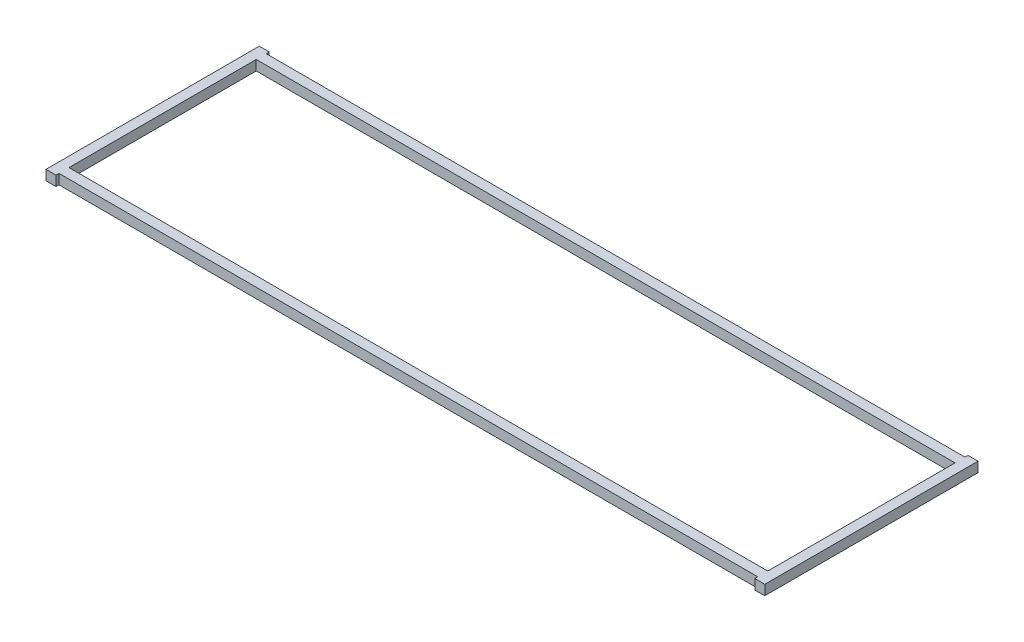
SolidWorks part; units mm, degrees
ref_plane "Front" through (0, 0, 0) normal (0, 0, 1) x (1, 0, 0)
ref_plane "Top" through (0, 0, 0) normal (0, 1, 0) x (1, 0, 0)
ref_plane "Right" through (0, 0, 0) normal (1, 0, 0) x (0, 0, -1)
sketch "Sketch1" plane through (0, 0, 0) normal (0, 1, 0) x (1, 0, 0)
  line L0 (222.25, 67.8212) -> (228.6, 67.8212)
  line L1 (-228.6, 67.8212) -> (-222.25, 67.8212)
  line L2 (-228.6, 67.8212) -> (-228.6, -67.8212)
  line L3 (-228.6, -67.8212) -> (-222.25, -67.8212)
  line L4 (228.6, 67.8212) -> (228.6, -67.8212)
  line L5 (-228.6, 67.8212) -> (228.6, -67.8212) construction
  line L6 (-228.6, -67.8212) -> (228.6, 67.8212) construction
  line L8 (-222.25, 67.8212) -> (-222.25, 65.913)
  line L9 (-222.25, 65.913) -> (222.25, 65.913)
  line L10 (222.25, 67.8212) -> (222.25, 65.913)
  line L12 (-222.25, -67.8212) -> (-222.25, -65.913)
  line L13 (-222.25, -65.913) -> (222.25, -65.913)
  line L14 (222.25, -67.8212) -> (222.25, -65.913)
  line L15 (222.25, -67.8212) -> (228.6, -67.8212)
  line L17 (-222.25, -59.563) -> (222.25, -59.563)
  line L18 (-222.25, -59.563) -> (-222.25, 59.563)
  line L19 (-222.25, 59.563) -> (222.25, 59.563)
  line L20 (222.25, -59.563) -> (222.25, 59.563)
  line L21 (-222.25, -59.563) -> (222.25, 59.563) construction
  line L22 (-222.25, 59.563) -> (222.25, -59.563) construction
  point P0 (0, 0)
  point P14 (0, 0)
  dimension "D1" = 457.2
  dimension "D2" = 135.6423
  dimension "D3" = 6.35
  dimension "D4" = 6.35
  dimension "D6" = 6.35
  dimension "D7" = 6.35
  dimension "D5" = 1.9082
extrude "Boss-Extrude1" add sketch "Sketch1" along normal blind 6.35
sketch "Sketch2" [suppressed] plane through (0, 6.35, 0) normal (0, 1, 0) x (1, 0, 0)
  line L24 (222.1484, -58.7851) -> (228.7016, -58.7851)
  line L25 (228.7016, -58.7851) -> (228.7016, 58.7851)
  line L26 (228.7016, 58.7851) -> (222.1484, 58.7851)
  line L27 (222.1484, 58.7851) -> (222.1484, 56.8769)
  line L28 (222.1484, 56.8769) -> (-222.1484, 56.8769)
  line L29 (-222.1484, 56.8769) -> (-222.1484, 58.7851)
  line L30 (-222.1484, 58.7851) -> (-228.7016, 58.7851)
  line L31 (-228.7016, 58.7851) -> (-228.7016, -58.7851)
  line L32 (-228.7016, -58.7851) -> (-222.1484, -58.7851)
  line L33 (-222.1484, -58.7851) -> (-222.1484, -56.877)
  line L34 (-222.1484, -56.877) -> (222.1484, -56.877)
  line L35 (222.1484, -56.877) -> (222.1484, -58.7851)
  line L36 (222.1484, -58.7851) -> (228.7016, -58.7851)
  line L37 (228.7016, -58.7851) -> (228.7016, 58.7851)
  line L38 (228.7016, 58.7851) -> (222.1484, 58.7851)
  line L39 (222.1484, 58.7851) -> (222.1484, 56.8769)
  line L40 (222.1484, 56.8769) -> (-222.1484, 56.8769)
  line L41 (-222.1484, 56.8769) -> (-222.1484, 58.7851)
  line L42 (-222.1484, 58.7851) -> (-228.7016, 58.7851)
  line L43 (-228.7016, 58.7851) -> (-228.7016, -58.7851)
  line L44 (-228.7016, -58.7851) -> (-222.1484, -58.7851)
  line L45 (-222.1484, -58.7851) -> (-222.1484, -56.877)
  line L46 (-222.1484, -56.877) -> (222.1484, -56.877)
  line L47 (222.1484, -56.877) -> (222.1484, -58.7851)
  line L50 (222.1484, -50.3237) -> (222.1484, 50.3237)
  line L51 (-222.1484, -50.3237) -> (222.1484, -50.3237)
  line L52 (-222.1484, 50.3237) -> (-222.1484, -50.3237)
  line L53 (222.1484, 50.3237) -> (-222.1484, 50.3237)
  line L54 (222.1484, -50.3237) -> (222.1484, 50.3237)
  line L55 (-222.1484, -50.3237) -> (222.1484, -50.3237)
  line L56 (-222.1484, 50.3237) -> (-222.1484, -50.3237)
  line L57 (222.1484, 50.3237) -> (-222.1484, 50.3237)
  dimension "D1" = 0.1016
  dimension "D2" = 0.1016
sketch "Sketch3" [suppressed] plane through (0, 6.35, 0) normal (0, 1, 0) x (1, 0, 0)
  line L24 (222.1484, -63.354) -> (228.7016, -63.354)
  line L25 (228.7016, -63.354) -> (228.7016, 63.3539)
  line L26 (228.7016, 63.3539) -> (222.1484, 63.3539)
  line L27 (222.1484, 63.3539) -> (222.1484, 61.4458)
  line L28 (222.1484, 61.4458) -> (-222.1484, 61.4458)
  line L29 (-222.1484, 61.4458) -> (-222.1484, 63.3539)
  line L30 (-222.1484, 63.3539) -> (-228.7016, 63.3539)
  line L31 (-228.7016, 63.3539) -> (-228.7016, -63.354)
  line L32 (-228.7016, -63.354) -> (-222.1484, -63.354)
  line L33 (-222.1484, -63.354) -> (-222.1484, -61.4458)
  line L34 (-222.1484, -61.4458) -> (222.1484, -61.4458)
  line L35 (222.1484, -61.4458) -> (222.1484, -63.354)
  line L36 (222.1484, -63.354) -> (228.7016, -63.354)
  line L37 (228.7016, -63.354) -> (228.7016, 63.3539)
  line L38 (228.7016, 63.3539) -> (222.1484, 63.3539)
  line L39 (222.1484, 63.3539) -> (222.1484, 61.4458)
  line L40 (222.1484, 61.4458) -> (-222.1484, 61.4458)
  line L41 (-222.1484, 61.4458) -> (-222.1484, 63.3539)
  line L42 (-222.1484, 63.3539) -> (-228.7016, 63.3539)
  line L43 (-228.7016, 63.3539) -> (-228.7016, -63.354)
  line L44 (-228.7016, -63.354) -> (-222.1484, -63.354)
  line L45 (-222.1484, -63.354) -> (-222.1484, -61.4458)
  line L46 (-222.1484, -61.4458) -> (222.1484, -61.4458)
  line L47 (222.1484, -61.4458) -> (222.1484, -63.354)
  line L50 (-222.1484, -54.8926) -> (222.1484, -54.8926)
  line L51 (222.1484, -54.8926) -> (222.1484, 54.8926)
  line L52 (222.1484, 54.8926) -> (-222.1484, 54.8926)
  line L53 (-222.1484, 54.8926) -> (-222.1484, -54.8926)
  line L54 (-222.1484, -54.8926) -> (222.1484, -54.8926)
  line L55 (222.1484, -54.8926) -> (222.1484, 54.8926)
  line L56 (222.1484, 54.8926) -> (-222.1484, 54.8926)
  line L57 (-222.1484, 54.8926) -> (-222.1484, -54.8926)
  dimension "D1" = 0.1016
  dimension "D2" = 0.1016
sketch "Sketch4" plane through (0, 6.35, 0) normal (0, 1, 0) x (1, 0, 0)
  line L24 (222.1484, -67.9228) -> (228.7016, -67.9228)
  line L25 (228.7016, -67.9228) -> (228.7016, 67.9228)
  line L26 (228.7016, 67.9228) -> (222.1484, 67.9228)
  line L27 (222.1484, 67.9228) -> (222.1484, 66.0146)
  line L28 (222.1484, 66.0146) -> (-222.1484, 66.0146)
  line L29 (-222.1484, 66.0146) -> (-222.1484, 67.9228)
  line L30 (-222.1484, 67.9228) -> (-228.7016, 67.9228)
  line L31 (-228.7016, 67.9228) -> (-228.7016, -67.9228)
  line L32 (-228.7016, -67.9228) -> (-222.1484, -67.9228)
  line L33 (-222.1484, -67.9228) -> (-222.1484, -66.0146)
  line L34 (-222.1484, -66.0146) -> (222.1484, -66.0146)
  line L35 (222.1484, -66.0146) -> (222.1484, -67.9228)
  line L36 (222.1484, -67.9228) -> (228.7016, -67.9228)
  line L37 (228.7016, -67.9228) -> (228.7016, 67.9228)
  line L38 (228.7016, 67.9228) -> (222.1484, 67.9228)
  line L39 (222.1484, 67.9228) -> (222.1484, 66.0146)
  line L40 (222.1484, 66.0146) -> (-222.1484, 66.0146)
  line L41 (-222.1484, 66.0146) -> (-222.1484, 67.9228)
  line L42 (-222.1484, 67.9228) -> (-228.7016, 67.9228)
  line L43 (-228.7016, 67.9228) -> (-228.7016, -67.9228)
  line L44 (-228.7016, -67.9228) -> (-222.1484, -67.9228)
  line L45 (-222.1484, -67.9228) -> (-222.1484, -66.0146)
  line L46 (-222.1484, -66.0146) -> (222.1484, -66.0146)
  line L47 (222.1484, -66.0146) -> (222.1484, -67.9228)
  line L50 (222.1484, -59.4614) -> (222.1484, 59.4614)
  line L51 (-222.1484, -59.4614) -> (222.1484, -59.4614)
  line L52 (-222.1484, 59.4614) -> (-222.1484, -59.4614)
  line L53 (222.1484, 59.4614) -> (-222.1484, 59.4614)
  line L54 (222.1484, -59.4614) -> (222.1484, 59.4614)
  line L55 (-222.1484, -59.4614) -> (222.1484, -59.4614)
  line L56 (-222.1484, 59.4614) -> (-222.1484, -59.4614)
  line L57 (222.1484, 59.4614) -> (-222.1484, 59.4614)
  dimension "D1" = 0.1016
  dimension "D2" = 0.1016
equation "\"D2@Sketch1\"       = (4.87075-.25) + 2 * ( 0.25 + ( 6 / 64 ) + 0.016 )"
